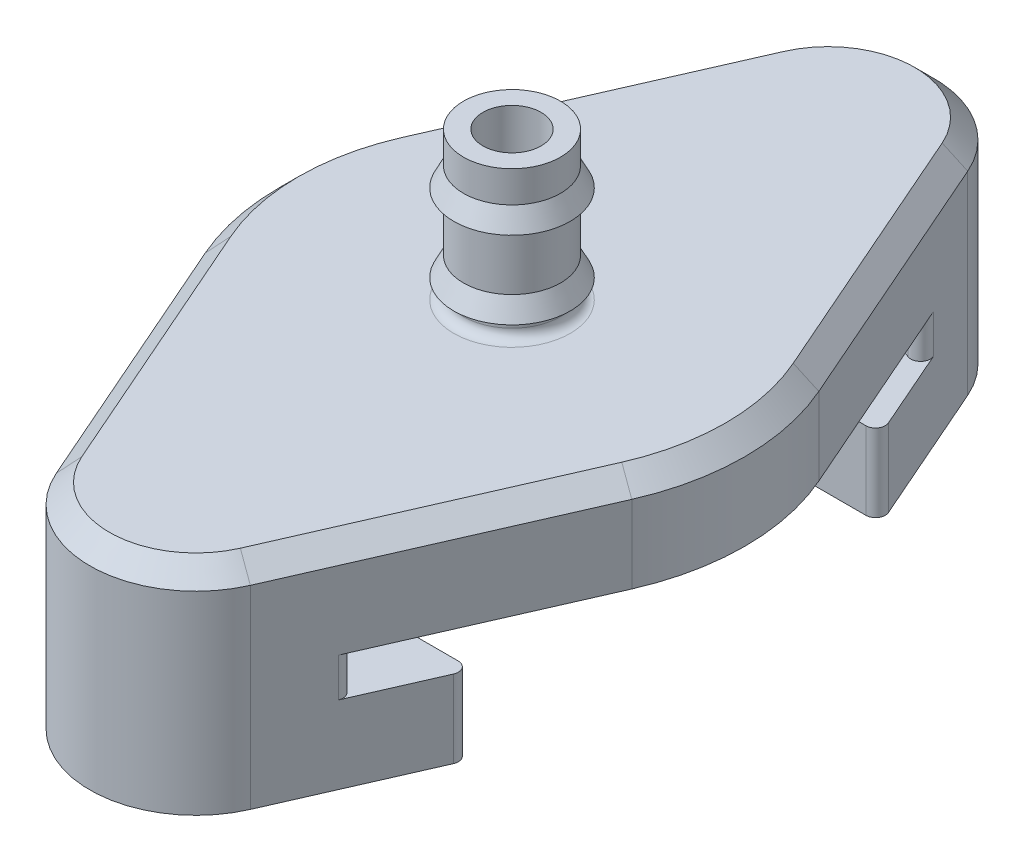
SolidWorks part; units mm, degrees
ref_plane "Front Plane" through (0, 0, 0) normal (0, 0, 1) x (1, 0, 0)
ref_plane "Top Plane" through (0, 0, 0) normal (0, 1, 0) x (1, 0, 0)
ref_plane "Right Plane" through (0, 0, 0) normal (1, 0, 0) x (0, 0, -1)
sketch "Sketch2" plane through (0, 0, 0) normal (1, 0, 0) x (0, 0, -1)
  line L0 (-1.5, 0) -> (0, 0) construction
  line L5 (-2.5, 0) -> (-21.75, 0)
  line L7 (-1.5, -5) -> (-15.75, -5)
  line L8 (-21.75, 0) -> (-21.75, -11)
  line L11 (-21.75, -11) -> (-8.75, -11)
  line L12 (-15.75, -5) -> (-15.75, -7)
  line L15 (-15.75, -7) -> (-8.75, -7)
  line L16 (-8.75, -11) -> (-8.75, -7)
  line L17 (-1.5, 6) -> (-1.5, -5)
  line L19 (-2.5, 0) -> (-2.5, 1)
  line L22 (-2.5, 6) -> (-3, 5)
  line L23 (-3, 5) -> (-2.5, 5)
  line L24 (-2.5, 2) -> (-3, 1)
  line L25 (-3, 1) -> (-2.5, 1)
  line L26 (-2.5, 2) -> (-2.5, 5)
  line L37 (0, 7.88) -> (0, -7.88) construction
  line L38 (-2.5, 6) -> (-2.5, 7.6164)
  line L39 (-2.5, 7.6164) -> (-1.5, 7.6164)
  line L40 (-1.5, 7.6164) -> (-1.5, 6)
  dimension "D2" = 2
  dimension "D3" = 6
  dimension "D4" = 4
  dimension "D1" = 15.75
  dimension "D5" = 0.5
  dimension "D9" = 1
  dimension "D10" = 3
  dimension "D15" = 8.75
  dimension "D6" = 2.5
  dimension "D7" = 1
  dimension "D11" = 1
  dimension "D12" = 5
revolve "Revolve1" add sketch "Sketch2" angle 360 about L37
sketch "Sketch3" plane through (0, 0, 0) normal (0, 1, 0) x (1, 0, 0)
  line L0 (-10.9903, 4.818) -> (-5, 18.4826)
  line L1 (5, 18.4826) -> (10.9903, 4.818)
  line L2 (-10.9903, -4.818) -> (-5, -18.4826)
  line L3 (5, -18.4826) -> (10.9903, -4.818)
  line L4 (0, 16.2907) -> (0, -16.2907) construction
  arc A0 (-10.9903, -4.818) -> (-10.9903, 4.818) centre (0, 0) cw
  arc A1 (10.9903, 4.818) -> (10.9903, -4.818) centre (0, 0) cw
  arc A2 (-5, 18.4826) -> (5, 18.4826) centre (0, 16.2907) cw
  arc A3 (-5, -18.4826) -> (5, -18.4826) centre (0, -16.2907) ccw
  circle A4 centre (0, 0) radius 21.75 construction
  circle A10 centre (0, 0) radius 21.75
  point P12 (0, 0)
  circle M11 centre (0, 0) radius 21.75
  dimension "D1" = 12
  dimension "D2" = 12
  dimension "D4" = 5
extrude "Cut-Extrude1" cut sketch "Sketch3" against normal through all contours A3 L2 A0 L0 A2 M11 | A3 A2 L1 A1 L3 M11
sketch "Sketch5" plane through (0, -11, 0) normal (0, -1, 0) x (1, 0, 0)
  line L5 (-12, 10.5) -> (12, -10.5) construction
  line L6 (-12, 10.5) -> (12, 10.5)
  line L7 (-12, 10.5) -> (-12, -10.5)
  line L8 (-12, -10.5) -> (12, -10.5)
  line L9 (12, 10.5) -> (12, -10.5)
  arc A13 (-10.9903, 4.818) -> (-10.9903, -4.818) centre (0, 0) ccw construction
  point P0 (0, 0)
  dimension "D5" = 21
extrude "Cut-Extrude3" cut sketch "Sketch5" against normal up to surface (6 mm away) up to face at (0, -5, 1.5)
fillet "Fillet1" radius 0.5 8 edges at (-6.8946, -6, 14.1608) (6.8946, -6, -14.1608) (-6.8946, -6, -14.1608) (6.8946, -6, 14.1608) (-8.4994, -9, -10.5) (8.4994, -9, -10.5) (-8.4994, -9, 10.5) (8.4994, -9, 10.5)
fillet "Fillet3" radius 0.5 1 edges at (0, 0, 2.5)
sketch "Sketch11" plane through (0, 0, 0) normal (1, 0, 0) x (0, 0, -1)
  line L1 (-17.0456, -1.5) -> (17.0456, -1.5)
  line L2 (-17.0456, -1.5) -> (-17.0456, -15.1462)
  line L3 (-17.0456, -15.1462) -> (17.0456, -15.1462)
  line L4 (17.0456, -1.5) -> (17.0456, -15.1462)
  line L5 (-17.0456, -1.5) -> (17.0456, -15.1462) construction
  line L6 (-17.0456, -15.1462) -> (17.0456, -1.5) construction
  point P0 (0, -8.3231)
  dimension "D1" = 1.5
extrude "Cut-Extrude6" [suppressed] cut sketch "Sketch11" against normal through all both and the other way through all
chamfer "Chamfer2" distance 1 angle 45 8 edges at (-7.9952, 0, -11.6503) (-12, 0, 0) (0, 0, -21.75) (-7.9952, 0, 11.6503) (7.9952, 0, -11.6503) (0, 0, 21.75) (12, 0, 0) (7.9952, 0, 11.6503)
sketch "Sketch12" plane through (0, -11, 0) normal (0, -1, 0) x (1, 0, 0)
  line L0 (0, 21.75) -> (0, -21.75) construction
  arc A0 (5, 18.4826) -> (-5, 18.4826) centre (0, 16.2907) ccw construction
  arc A1 (-5, -18.4826) -> (5, -18.4826) centre (0, -16.2907) ccw construction
  circle A2 centre (0, -13.25) radius 1.4
  circle A3 centre (0, 13.25) radius 1.4
  dimension "D1" = 2.8
  dimension "D2" = 2.8
  dimension "D3" = 8.5
  dimension "D4" = 8.5
extrude "Cut-Extrude7" cut sketch "Sketch12" against normal up to surface (6 mm away) up to face at (0, -5, 0)
sketch "Sketch13" plane through (0, -5, 0) normal (0, -1, 0) x (1, 0, 0)
  circle A0 centre (0, 0) radius 7.375
  dimension "D1" = 14.75
extrude "Cut-Extrude8" cut sketch "Sketch13" against normal blind 2
sketch "Sketch14" plane through (0, -5, 0) normal (0, -1, 0) x (1, 0, 0)
  circle A0 centre (0, 0) radius 6.75
  circle A1 centre (0, 0) radius 7.375 construction
  circle A2 centre (0, 0) radius 7.375
  dimension "D1" = 13.5
extrude "Boss-Extrude1" add sketch "Sketch14" against normal blind 1 separate body
combine bodies "Combine1" operation type add bodies to combine 112 113
equation "\"syringeOuterRadius\"= 31"
equation "\"syringeTubeRadius\"= 17"
equation "\"syringeTubeInnerRadius\"= 15"
equation "\"D1@Sketch2\"=(\"syringeOuterRadius\"+0.5)/2"
